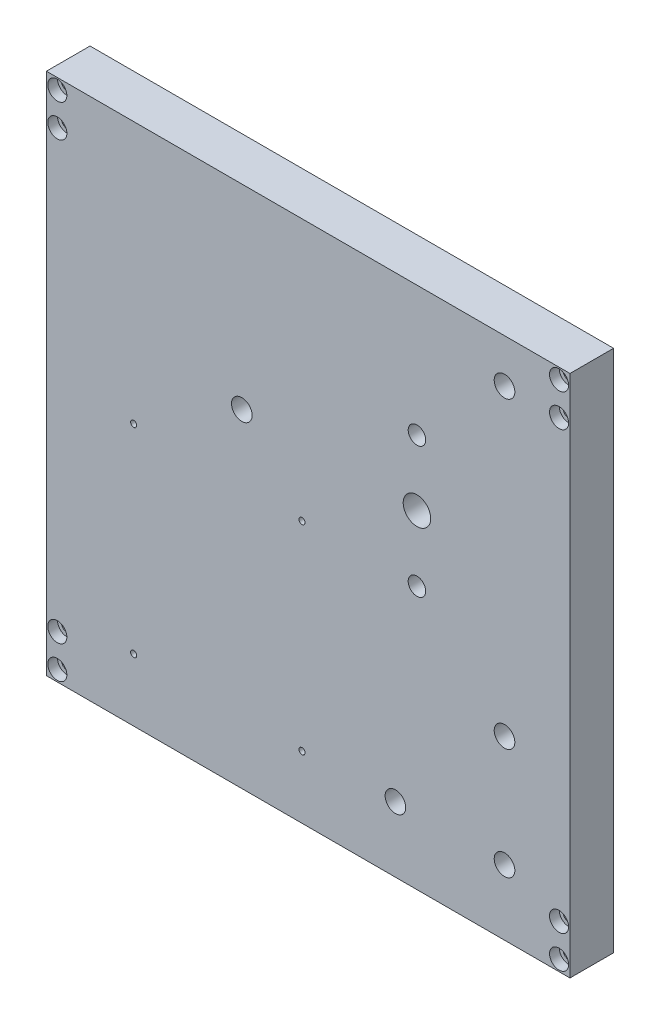
SolidWorks part; units mm, degrees
ref_plane "Front Plane" through (0, 0, 0) normal (0, 0, 1) x (1, 0, 0)
ref_plane "Top Plane" through (0, 0, 0) normal (0, 1, 0) x (1, 0, 0)
ref_plane "Right Plane" through (0, 0, 0) normal (1, 0, 0) x (0, 0, -1)
sketch "Sketch1" plane through (0, 0, 0) normal (0, 0, 1) x (1, 0, 0)
  line L1 (-76.2, -76.2) -> (76.2, -76.2)
  line L2 (-76.2, -76.2) -> (-76.2, 76.2)
  line L3 (-76.2, 76.2) -> (76.2, 76.2)
  line L4 (76.2, -76.2) -> (76.2, 76.2)
  line L5 (-76.2, -76.2) -> (76.2, 76.2) construction
  line L6 (-76.2, 76.2) -> (76.2, -76.2) construction
  point P0 (0, 0)
  dimension "D1" = 152.4
  dimension "D2" = 152.4
extrude "Boss-Extrude1" add sketch "Sketch1" along normal blind 12.7 contours L3 L4 L1 L2
ref_plane "Plane1" through (0, 0, 0) normal (-1, 0, 0) x (0, 0, 1)
ref_plane "Plane2" through (0, 0, 0) normal (0, 1, 0) x (1, 0, 0)
hole_wizard "#2-56 Tapped Hole1" positions "Sketch8" profile "Sketch9" tap size "#2-56" standard "ANSI Inch" end condition through all
sketch "Sketch8" plane through (0, 0, 12.7) normal (0, 0, 1) x (1, 0, 0)
  line L2 (-76.2, -76.2) -> (-76.2, 76.2) construction
  line L3 (-76.2, 76.2) -> (76.2, 76.2) construction
  point P0 (-50.8, 0)
  point P20 (-50.8, -58)
  point P23 (-1.8, -58)
  point P26 (-1.8, 0)
  dimension "D1" = 25.4
  dimension "D2" = 76.2
  dimension "D3" = 58
  dimension "D4" = 49
  dimension "D5" = 58
  dimension "D6" = 49
sketch "Sketch9" plane through (-50.8, 0, 12.7) normal (1, 0, 0) x (0, -1, 0)
  line L0 (0, 0) -> (0, 12.7)
  line L1 (0, 12.7) -> (0.889, 12.7)
  line L2 (0.889, 12.7) -> (0.889, 0)
  line L5 (0.889, 0) -> (0, 0)
  line L11 (0, -6.35) -> (0, 107.95) construction
  dimension "Thread Major Dia." = 1.778
  dimension "Thru Tap Drill Depth" = 12.7
hole_wizard "CBORE for #4 Socket Head Cap Screw1" positions "Sketch10" profile "Sketch12" counterbore size "#4" standard "ANSI Inch" end condition through all
sketch "Sketch10" plane through (0, 0, 12.7) normal (0, 0, 1) x (1, 0, 0)
  line L0 (-76.2, -76.2) -> (-76.2, 76.2) construction
  line L1 (-76.2, 76.2) -> (76.2, 76.2) construction
  line L2 (0, 3.4925) -> (0, -3.4925) construction
  line L3 (3.4925, 0) -> (-3.4925, 0) construction
  point P0 (-73.025, 63.5)
  point P2 (-73.025, 73.025)
  point P11 (73.025, 63.5)
  point P12 (73.025, 73.025)
  point P16 (73.025, -63.5)
  point P17 (73.025, -73.025)
  point P18 (-73.025, -63.5)
  point P19 (-73.025, -73.025)
  dimension "D1" = 3.175
  dimension "D2" = 3.175
  dimension "D3" = 3.175
  dimension "D4" = 12.7
sketch "Sketch12" plane through (-73.025, 63.5, 12.7) normal (1, 0, 0) x (0, -1, 0)
  line L0 (0, 0) -> (0, 12.7)
  line L1 (0, 12.7) -> (1.6319, 12.7)
  line L3 (1.6319, 12.7) -> (1.6319, 2.8448)
  line L4 (1.6319, 2.8448) -> (2.7788, 2.8448)
  line L5 (2.7788, 2.8448) -> (2.7788, 0)
  line L7 (2.7788, 0) -> (0, 0)
  line L11 (0, -6.35) -> (0, 107.95) construction
  dimension "Thru Hole Dia." = 3.2639
  dimension "Thru Hole Depth" = 12.7
  dimension "C'Bore Dia." = 5.5575
  dimension "C'Bore Depth" = 2.8448
hole_wizard "Ø6.0mm Dowel Hole1" positions "Sketch13" profile "Sketch14" hole size "Ø6.0" standard "ANSI Metric" end condition through all
sketch "Sketch13" plane through (0, 0, 12.7) normal (0, 0, 1) x (1, 0, 0)
  line L0 (-76.2, 76.2) -> (76.2, 76.2) construction
  line L1 (76.2, -76.2) -> (76.2, 76.2) construction
  line L2 (-76.2, -76.2) -> (76.2, -76.2) construction
  point P0 (57.15, 63.5)
  point P2 (57.15, -24.801)
  point P4 (-19.3209, 19.3495)
  point P15 (57.15, -57.15)
  point P17 (25.4, -57.15)
  dimension "D1" = 88.301
  dimension "D2" = 12.7
  dimension "D3" = 88.301
  dimension "D4" = 88.301
  dimension "D5" = 19.05
  dimension "D6" = 19.05
  dimension "D7" = 19.05
  dimension "D8" = 19.05
  dimension "D9" = 19.05
  dimension "D10" = 31.75
sketch "Sketch14" plane through (57.15, 63.5, 12.7) normal (1, 0, 0) x (0, -1, 0)
  line L0 (0, 0) -> (0, 12.7)
  line L1 (0, 12.7) -> (3, 12.7)
  line L2 (3, 12.7) -> (3, 0)
  line L5 (3, 0) -> (0, 0)
  line L11 (0, -6.35) -> (0, 107.95) construction
  dimension "Thru Hole Dia." = 6
  dimension "Thru Hole Depth" = 12.7
sketch "Sketch17" plane through (0, 0, 12.7) normal (0, 0, 1) x (1, 0, 0)
  circle A3 centre (31.6597, 19.3495) radius 47.9806
hole_wizard "Ø8.0mm Dowel Hole1" positions "Sketch15" profile "Sketch16" hole size "Ø8.0" standard "ANSI Metric" end condition through all
sketch "Sketch15" plane through (0, 0, 12.7) normal (0, 0, 1) x (1, 0, 0)
  circle A0 centre (31.6597, 19.3495) radius 47.9806 construction
  point P0 (31.6597, 19.3495)
  dimension "D1" = 0
sketch "Sketch16" plane through (31.6597, 19.3495, 12.7) normal (1, 0, 0) x (0, -1, 0)
  line L0 (0, 0) -> (0, 12.7)
  line L1 (0, 12.7) -> (4, 12.7)
  line L2 (4, 12.7) -> (4, 0)
  line L5 (4, 0) -> (0, 0)
  line L11 (0, -6.35) -> (0, 107.95) construction
  dimension "Thru Hole Dia." = 8
  dimension "Thru Hole Depth" = 12.7
hole_wizard "1/4-20 Tapped Hole1" positions "Sketch18" profile "Sketch19" tap size "1/4-20" standard "ANSI Inch" end condition through all
sketch "Sketch18" plane through (0, 0, 12.7) normal (0, 0, 1) x (1, 0, 0)
  point P0 (31.6597, 0.2995)
  point P2 (31.6597, 38.3995)
  dimension "D1" = 38.1
  dimension "D2" = 19.05
  dimension "D3" = 0
  dimension "D4" = 19.05
sketch "Sketch19" plane through (31.6597, 0.2995, 12.7) normal (1, 0, 0) x (0, -1, 0)
  line L0 (0, 0) -> (0, 12.7)
  line L1 (0, 12.7) -> (2.5527, 12.7)
  line L2 (2.5527, 12.7) -> (2.5527, 0)
  line L5 (2.5527, 0) -> (0, 0)
  line L11 (0, -6.35) -> (0, 107.95) construction
  dimension "Thru Tap Drill Dia." = 5.1054
  dimension "Thru Tap Drill Depth" = 12.7
cosmetic thread "Hole Thread1"
cosmetic thread "Hole Thread2"
